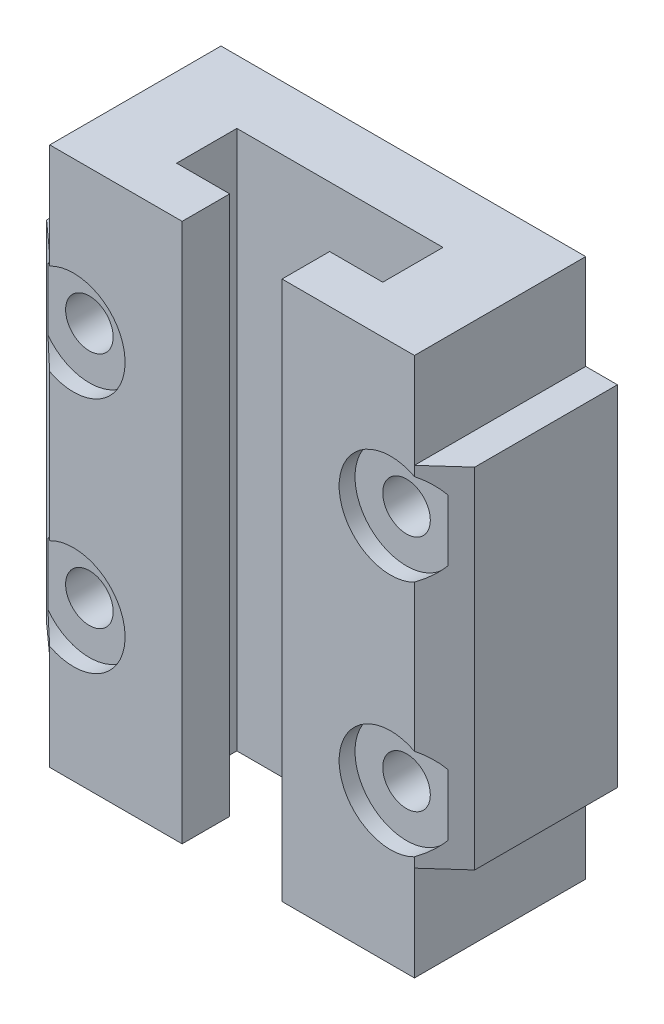
SolidWorks part; units mm, degrees
ref_plane "前视基准面" through (0, 0, 0) normal (0, 0, 1) x (1, 0, 0)
ref_plane "上视基准面" through (0, 0, 0) normal (0, 1, 0) x (1, 0, 0)
ref_plane "右视基准面" through (0, 0, 0) normal (1, 0, 0) x (0, 0, -1)
sketch "草图1" plane through (0, 0, 0) normal (0, 1, 0) x (1, 0, 0)
  line L1 (-11.5, -5.4) -> (11.5, -5.4)
  line L2 (-11.5, -5.4) -> (-11.5, 5.4)
  line L3 (-11.5, 5.4) -> (11.5, 5.4)
  line L4 (11.5, -5.4) -> (11.5, 5.4)
  line L5 (-11.5, -5.4) -> (11.5, 5.4) construction
  line L6 (-11.5, 5.4) -> (11.5, -5.4) construction
  point P0 (0, 0)
  dimension "D1" = 23
  dimension "D2" = 10.8
extrude "凸台-拉伸1" add sketch "草图1" along normal blind 34
sketch "草图2" plane through (0, 34, 0) normal (0, 1, 0) x (1, 0, 0)
  line L0 (0, 6.403) -> (0, -9.5972) construction
  line L1 (-6.5, 1.4) -> (6.5, 1.4)
  line L2 (6.5, 1.4) -> (6.5, -2.4)
  line L3 (6.5, -2.4) -> (3.15, -2.4)
  line L4 (3.15, -2.4) -> (3.15, -5.4)
  line L5 (-11.5, -5.4) -> (11.5, -5.4) construction
  line L6 (3.15, -5.4) -> (-3.15, -5.4)
  line L7 (-6.5, -2.4) -> (-3.15, -2.4)
  line L8 (-6.5, 1.4) -> (-6.5, -2.4)
  line L9 (-3.15, -2.4) -> (-3.15, -5.4)
  line L10 (11.5, 5.4) -> (-11.5, 5.4) construction
  point P12 (0, -5.4)
  point P15 (0, 1.4)
  dimension "D1" = 6.3
  dimension "D2" = 13
  dimension "D3" = 3
  dimension "D4" = 4
extrude "切除-拉伸1" cut sketch "草图2" against normal through all
sketch "草图3" plane through (0, 0, -5.4) normal (0, 0, -1) x (-1, 0, 0)
  line L0 (-11.5, 17) -> (11.5, 17) construction
  line L1 (-11.5, 34) -> (-11.5, 0) construction
  line L2 (11.5, 34) -> (11.5, 0) construction
  line L3 (0, 34) -> (0, 0) construction
  line L4 (-11.5, 34) -> (11.5, 34) construction
  line L5 (13.5, 28) -> (6.5, 6) construction
  line L6 (-13.5, 6) -> (-6.5, 6)
  line L7 (-13.5, 6) -> (-13.5, 28)
  line L8 (-13.5, 28) -> (-6.5, 28)
  line L9 (-6.5, 6) -> (-6.5, 28)
  line L10 (-13.5, 6) -> (-6.5, 28) construction
  line L11 (-13.5, 28) -> (-6.5, 6) construction
  line L12 (13.5, 6) -> (6.5, 28) construction
  line L13 (6.5, 6) -> (6.5, 28)
  line L14 (13.5, 28) -> (6.5, 28)
  line L15 (13.5, 6) -> (13.5, 28)
  line L16 (13.5, 6) -> (6.5, 6)
  point P6 (-10, 17)
  point P20 (10, 17)
  dimension "D1" = 22
  dimension "D2" = 7
  dimension "D3" = 27
extrude "凸台-拉伸2" add sketch "草图3" against normal blind 9
sketch "草图5" plane through (0, 6, 0) normal (0, -1, 0) x (1, 0, 0)
  line L0 (11.5, 5.4) -> (11.5, 3.6)
  line L1 (11.5, 3.6) -> (13.5, 3.6)
  line L2 (13.5, 3.6) -> (11.5, 5.4)
  line L3 (0, 6.7778) -> (0, -7.3778) construction
  line L4 (-13.5, 3.6) -> (-11.5, 5.4)
  line L5 (-11.5, 3.6) -> (-13.5, 3.6)
  line L6 (-11.5, 5.4) -> (-11.5, 3.6)
extrude "凸台-拉伸3" add sketch "草图5" against normal up to surface (22 mm away) up to face at (-12.5, 28, -0.9)
sketch "草图7" plane through (0, 0, 5.4) normal (0, 0, 1) x (1, 0, 0)
  line L0 (-13.5, 17) -> (13.5, 17) construction
  line L1 (-13.5, 6) -> (-13.5, 28) construction
  line L2 (13.5, 28) -> (13.5, 6) construction
  line L3 (0, 34) -> (0, 0) construction
  line L4 (6.5, 34) -> (-6.5, 34) construction
  circle A0 centre (-10, 24.5) radius 3.25
  circle A1 centre (-10, 9.5) radius 3.25
  circle A2 centre (10, 9.5) radius 3.25
  circle A3 centre (10, 24.5) radius 3.25
  dimension "D1" = 10
  dimension "D2" = 7.5
  dimension "D3" = 6.5
extrude "切除-拉伸7" cut sketch "草图7" against normal blind 1
sketch "草图8" plane through (0, 0, 4.4) normal (0, 0, 1) x (1, 0, 0)
  circle A0 centre (-10, 24.5) radius 1.5
  circle A1 centre (10, 24.5) radius 1.5
  circle A2 centre (-10, 9.5) radius 1.5
  circle A3 centre (10, 9.5) radius 1.5
  dimension "D1" = 3
  dimension "D2" = 3
  dimension "D3" = 3
  dimension "D4" = 3
extrude "切除-拉伸8" cut sketch "草图8" against normal up to next
